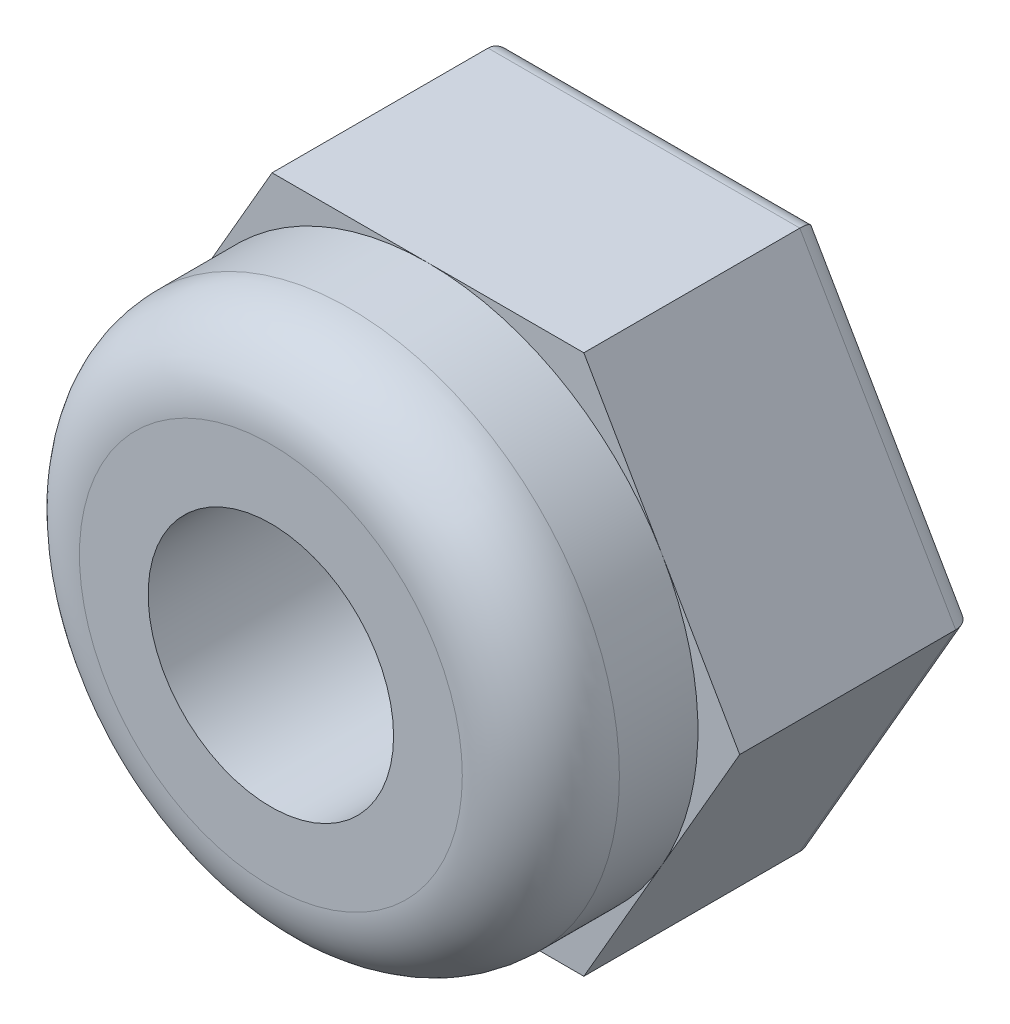
SolidWorks part; units mm, degrees
ref_plane "Front Plane" through (0, 0, 0) normal (0, 0, 1) x (1, 0, 0)
ref_plane "Top Plane" through (0, 0, 0) normal (0, 1, 0) x (1, 0, 0)
ref_plane "Right Plane" through (0, 0, 0) normal (1, 0, 0) x (0, 0, -1)
sketch "Sketch1" plane through (0, 0, 0) normal (0, 0, 1) x (1, 0, 0)
  line L1 (3.1754, 0) -> (1.5877, 2.75)
  line L2 (1.5877, 2.75) -> (-1.5877, 2.75)
  line L3 (-1.5877, 2.75) -> (-3.1754, 0)
  line L4 (-3.1754, 0) -> (-1.5877, -2.75)
  line L5 (-1.5877, -2.75) -> (1.5877, -2.75)
  line L6 (1.5877, -2.75) -> (3.1754, 0)
  circle A0 centre (0, 0) radius 2.75 construction
  circle A1 centre (0, 0) radius 1.25
  dimension "D1" = 5.5
  dimension "D2" = 2.5
extrude "Boss-Extrude1" add sketch "Sketch1" along normal blind 2.4
sketch "Sketch2" plane through (0, 0, 2.4) normal (0, 0, 1) x (1, 0, 0)
  circle A0 centre (0, 0) radius 1.25
  circle A1 centre (0, 0) radius 2.75
  circle A2 centre (0, 0) radius 1.25 construction
extrude "Boss-Extrude2" add sketch "Sketch2" along normal blind 1.6
fillet "Fillet1" radius 0.2 7 edges at (1.25, 0, 0) (2.3816, 1.375, 0) (0, 2.75, 0) (-2.3816, 1.375, 0) (-2.3816, -1.375, 0) (0, -2.75, 0) (2.3816, -1.375, 0)
fillet "Fillet2" radius 0.8 1 edges at (2.75, 0, 4)
